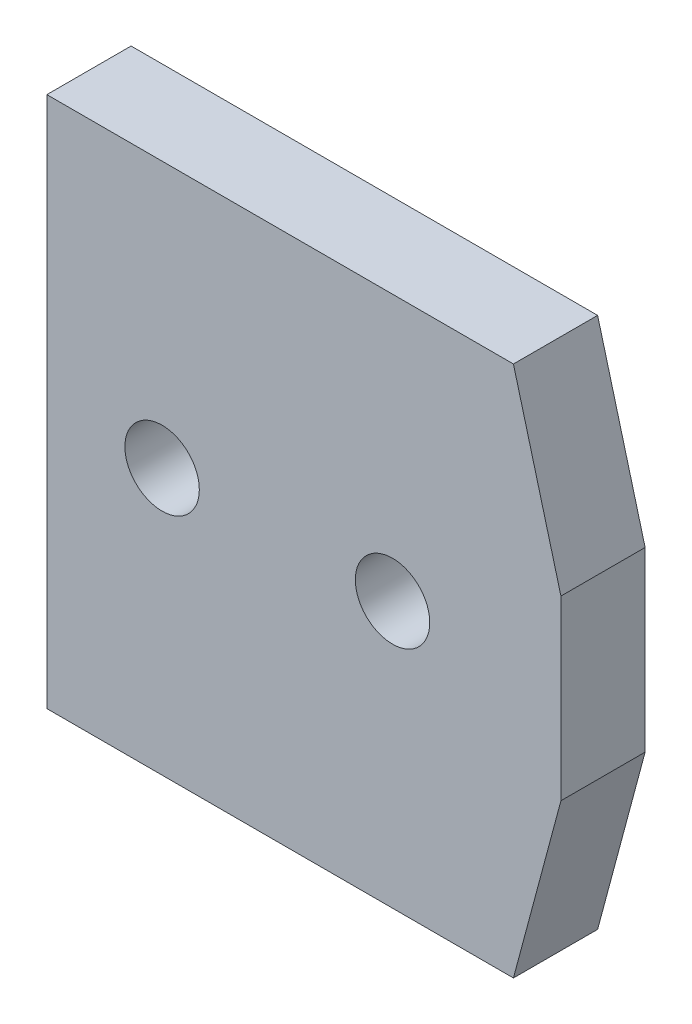
SolidWorks part; units mm, degrees
ref_plane "Ebene vorne" through (0, 0, 0) normal (0, 0, 1) x (1, 0, 0)
ref_plane "Ebene oben" through (0, 0, 0) normal (0, 1, 0) x (1, 0, 0)
ref_plane "Ebene rechts" through (0, 0, 0) normal (1, 0, 0) x (0, 0, -1)
sketch "Skizze1" plane through (0, 0, 0) normal (0, 0, 1) x (1, 0, 0)
  line L0 (-14.5, 15) -> (-14.5, -15) construction
  line L1 (-14.5, -15) -> (11.8205, -15) construction
  line L2 (11.8205, -15) -> (14.5, -5) construction
  line L3 (14.5, -5) -> (14.5, 5) construction
  line L4 (14.5, 5) -> (11.8205, 15) construction
  line L5 (11.8205, 15) -> (-14.5, 15) construction
  line L6 (-14.5, 15) -> (-14.5, -15)
  line L7 (-14.5, -15) -> (11.8205, -15)
  line L8 (11.8205, -15) -> (14.5, -5)
  line L9 (14.5, -5) -> (14.5, 5)
  line L10 (14.5, 5) -> (11.8205, 15)
  line L11 (11.8205, 15) -> (-14.5, 15)
  arc A0 (5, -1.621) -> (5, 1.621) centre (5, 0) ccw construction
  arc A2 (-8, 1.621) -> (-8, -1.621) centre (-8, 0) ccw construction
  circle A8 centre (5, 0) radius 2.1
  circle A9 centre (-8, 0) radius 2.1
  point P5 (-8, 0)
  point P10 (5, 0)
extrude "Aufsatz-Linear austragen1" add sketch "Skizze1" along normal blind 4.75 contours A8 | A9 | L6 L7 L8 L9 L10 L11
